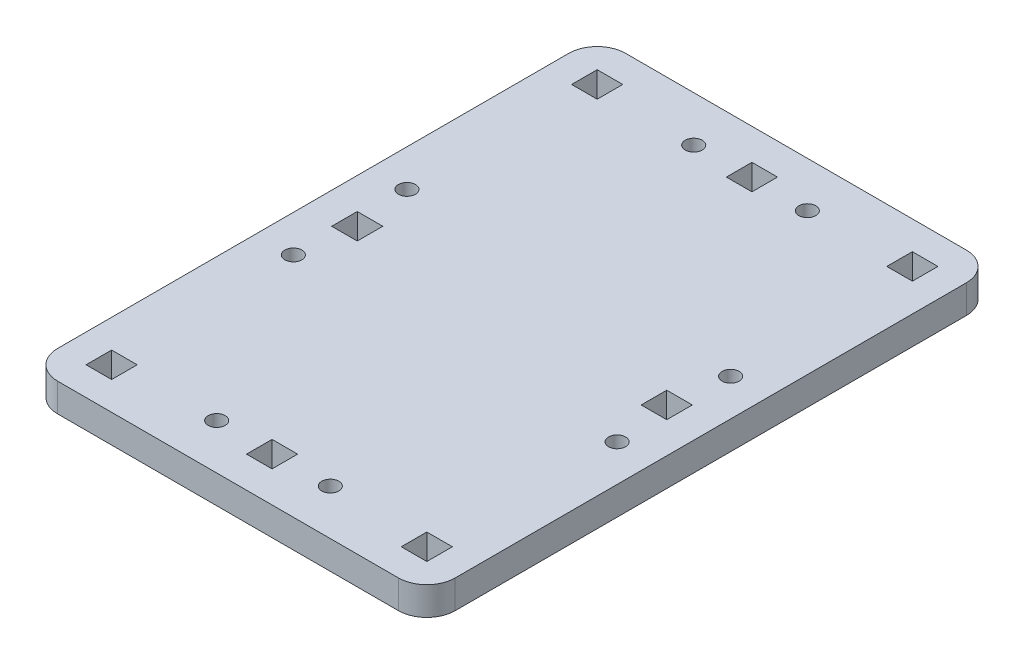
SolidWorks part; units mm, degrees
ref_plane "Front Plane" through (0, 0, 0) normal (0, 0, 1) x (1, 0, 0)
ref_plane "Top Plane" through (0, 0, 0) normal (0, 1, 0) x (1, 0, 0)
ref_plane "Right Plane" through (0, 0, 0) normal (1, 0, 0) x (0, 0, -1)
sketch "Sketch1" plane through (0, 0, 0) normal (0, 1, 0) x (1, 0, 0)
  line L0 (29.5, 2.25) -> (25, 2.25)
  line L1 (-30, 50) -> (30, 50)
  line L2 (-35, 45) -> (-35, -45)
  line L3 (-30, -50) -> (30, -50)
  line L4 (35, 45) -> (35, -45)
  line L5 (-2.25, -44.5) -> (2.25, -44.5)
  line L6 (-2.25, -44.5) -> (-2.25, -40)
  line L7 (-2.25, -40) -> (2.25, -40)
  line L8 (2.25, -44.5) -> (2.25, -40)
  line L9 (29.5, 2.25) -> (29.5, -2.25)
  line L10 (29.5, -2.25) -> (25, -2.25)
  line L11 (25, 2.25) -> (25, -2.25)
  line L12 (2.25, 40) -> (-2.25, 40)
  line L13 (-29.5, -2.25) -> (-25, -2.25)
  line L14 (-29.5, -2.25) -> (-29.5, 2.25)
  line L15 (-29.5, 2.25) -> (-25, 2.25)
  line L16 (-25, -2.25) -> (-25, 2.25)
  line L17 (-2.25, 44.5) -> (-2.25, 40)
  line L18 (2.25, 44.5) -> (-2.25, 44.5)
  line L19 (2.25, 44.5) -> (2.25, 40)
  line L20 (0, 50) -> (0, -50) construction
  line L21 (-54.7681, 0) -> (67.0693, 0) construction
  line L22 (30, -45) -> (30, -40.5)
  line L23 (30, -45) -> (25.5, -45)
  line L24 (25.5, -45) -> (25.5, -40.5)
  line L25 (30, 40.5) -> (25.5, 40.5)
  line L26 (-30, 45) -> (-25.5, 45)
  line L27 (-30, 45) -> (-30, 40.5)
  line L28 (-30, 40.5) -> (-25.5, 40.5)
  line L29 (-25.5, 45) -> (-25.5, 40.5)
  line L30 (25.5, 45) -> (25.5, 40.5)
  line L31 (30, 45) -> (25.5, 45)
  line L32 (30, 45) -> (30, 40.5)
  line L33 (-25.5, -45) -> (-25.5, -40.5)
  line L34 (-30, -40.5) -> (-25.5, -40.5)
  line L35 (-30, -45) -> (-30, -40.5)
  line L36 (-30, -45) -> (-25.5, -45)
  line L37 (30, -40.5) -> (25.5, -40.5)
  arc A0 (-35, -45) -> (-30, -50) centre (-30, -45) ccw
  arc A1 (30, -50) -> (35, -45) centre (30, -45) ccw
  arc A2 (30, 50) -> (35, 45) centre (30, 45) cw
  arc A3 (-30, 50) -> (-35, 45) centre (-30, 45) ccw
  circle A4 centre (10, 42) radius 1.5
  circle A5 centre (10, -42) radius 1.5
  circle A6 centre (-10, -42) radius 1.5
  circle A7 centre (-10, 42) radius 1.5
  circle A8 centre (28.5, 10) radius 1.5
  circle A9 centre (28.5, -10) radius 1.5
  circle A10 centre (-28.5, -10) radius 1.5
  circle A11 centre (-28.5, 10) radius 1.5
  point P6 (-35, -50)
  point P11 (35, 50)
  point P14 (-35, 50)
  point P35 (0, 0)
  dimension "D3" = 5
  dimension "D19" = 3
  dimension "D21" = 3
  dimension "D1" = 70
  dimension "D2" = 100
  dimension "D4" = 35
  dimension "D5" = 50
  dimension "D6" = 4.5
  dimension "D7" = 4.5
  dimension "D8" = 40
  dimension "D9" = 2.25
  dimension "D11" = 4.5
  dimension "D12" = 4.5
  dimension "D13" = 25
  dimension "D14" = 2.25
  dimension "D15" = 4.5
  dimension "D16" = 4.5
  dimension "D17" = 5
  dimension "D18" = 5
  dimension "D20" = 6.5
  dimension "D22" = 6.5
  dimension "D23" = 10
  dimension "D24" = 10
  dimension "D10" = 2
extrude "Boss-Extrude1" add sketch "Sketch1" along normal mid plane 5
equation "\"D20@Sketch1\"=\"D19@Sketch1\"/2 + 0.005"
equation "\"D21@Sketch1\"=\"D19@Sketch1\""
equation "\"D22@Sketch1\"=\"D20@Sketch1\""
equation "\"D24@Sketch1\"=\"D23@Sketch1\""
